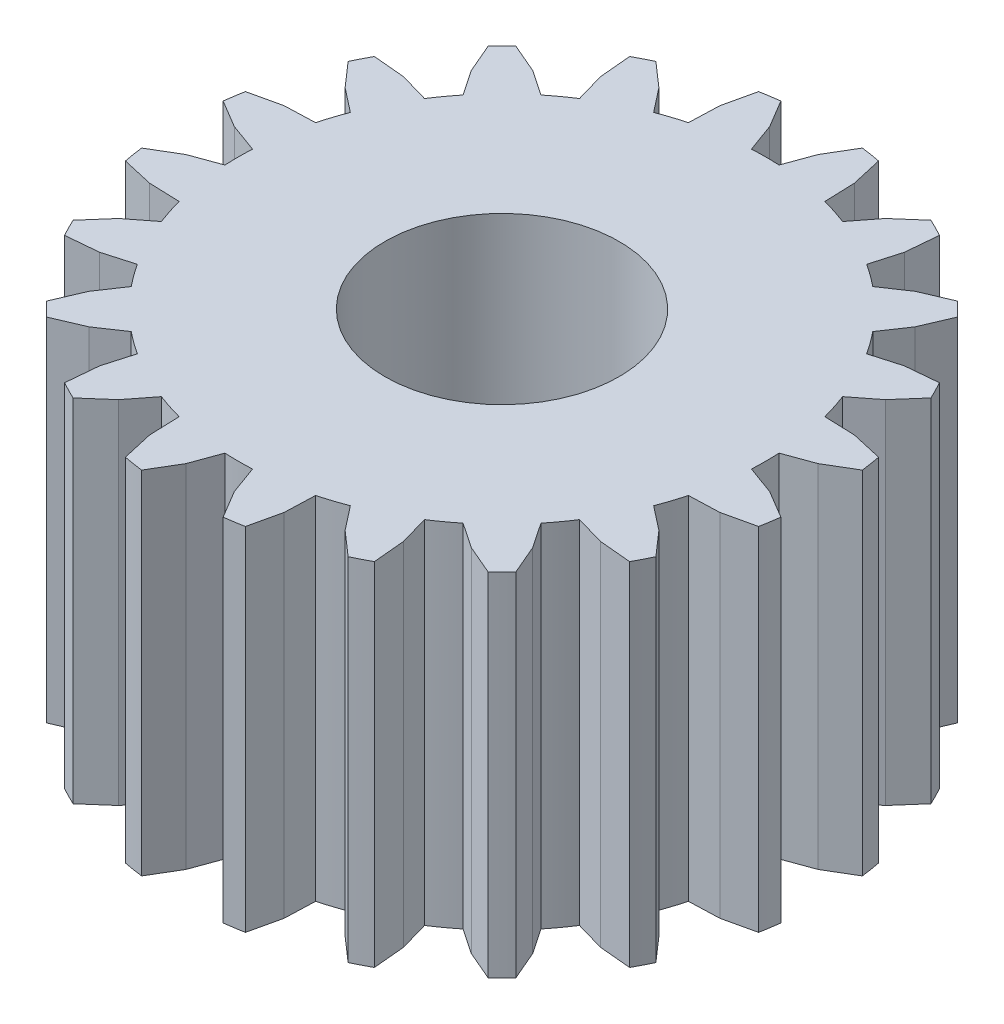
SolidWorks part; units mm, degrees
ref_plane "Ön Düzlem" through (0, 0, 0) normal (0, 0, 1) x (1, 0, 0)
ref_plane "Üst Düzlem" through (0, 0, 0) normal (0, 1, 0) x (1, 0, 0)
ref_plane "Sağ Düzlem" through (0, 0, 0) normal (1, 0, 0) x (0, 0, -1)
sketch "Çizim2" plane through (0, 0, 0) normal (0, 1, 0) x (1, 0, 0)
  line L0 (2.7279, -0.3477) -> (2.4914, -0.2068)
  line L1 (2.4914, -0.2068) -> (2.2469, -0.1178)
  line L2 (2.2469, 0.1178) -> (2.4914, 0.2068)
  line L3 (2.4914, 0.2068) -> (2.7279, 0.3477)
  line L4 (2.7019, 0.5123) -> (2.4334, 0.5733)
  line L5 (2.4334, 0.5733) -> (2.1733, 0.5823)
  line L6 (2.1006, 0.8063) -> (2.3056, 0.9665)
  line L7 (2.3056, 0.9665) -> (2.487, 1.1736)
  line L8 (2.4113, 1.3222) -> (2.1371, 1.2972)
  line L9 (2.1371, 1.2972) -> (1.887, 1.2254)
  line L10 (1.7486, 1.416) -> (1.8941, 1.6317)
  line L11 (1.8941, 1.6317) -> (2.0026, 1.8847)
  line L12 (1.8847, 2.0026) -> (1.6317, 1.8941)
  line L13 (1.6317, 1.8941) -> (1.416, 1.7486)
  line L14 (1.2254, 1.887) -> (1.2972, 2.1371)
  line L15 (1.2972, 2.1371) -> (1.3222, 2.4113)
  line L16 (1.1736, 2.487) -> (0.9665, 2.3056)
  line L17 (0.9665, 2.3056) -> (0.8063, 2.1006)
  line L18 (0.5823, 2.1733) -> (0.5733, 2.4334)
  line L19 (0.5733, 2.4334) -> (0.5123, 2.7019)
  line L20 (0.3477, 2.7279) -> (0.2068, 2.4914)
  line L21 (0.2068, 2.4914) -> (0.1178, 2.2469)
  line L22 (-0.1178, 2.2469) -> (-0.2068, 2.4914)
  line L23 (-0.2068, 2.4914) -> (-0.3477, 2.7279)
  line L24 (-0.5123, 2.7019) -> (-0.5733, 2.4334)
  line L25 (-0.5733, 2.4334) -> (-0.5823, 2.1733)
  line L26 (-0.8063, 2.1006) -> (-0.9665, 2.3056)
  line L27 (-0.9665, 2.3056) -> (-1.1736, 2.487)
  line L28 (-1.3222, 2.4113) -> (-1.2972, 2.1371)
  line L29 (-1.2972, 2.1371) -> (-1.2254, 1.887)
  line L30 (-1.416, 1.7486) -> (-1.6317, 1.8941)
  line L31 (-1.6317, 1.8941) -> (-1.8847, 2.0026)
  line L32 (-2.0026, 1.8847) -> (-1.8941, 1.6317)
  line L33 (-1.8941, 1.6317) -> (-1.7486, 1.416)
  line L34 (-1.887, 1.2254) -> (-2.1371, 1.2972)
  line L35 (-2.1371, 1.2972) -> (-2.4113, 1.3222)
  line L36 (-2.487, 1.1736) -> (-2.3056, 0.9665)
  line L37 (-2.3056, 0.9665) -> (-2.1006, 0.8063)
  line L38 (-2.1733, 0.5823) -> (-2.4334, 0.5733)
  line L39 (-2.4334, 0.5733) -> (-2.7019, 0.5123)
  line L40 (-2.7279, 0.3477) -> (-2.4914, 0.2068)
  line L41 (-2.4914, 0.2068) -> (-2.2469, 0.1178)
  line L42 (-2.2469, -0.1178) -> (-2.4914, -0.2068)
  line L43 (-2.4914, -0.2068) -> (-2.7279, -0.3477)
  line L44 (-2.7019, -0.5123) -> (-2.4334, -0.5733)
  line L45 (-2.4334, -0.5733) -> (-2.1733, -0.5823)
  line L46 (-2.1006, -0.8063) -> (-2.3056, -0.9665)
  line L47 (-2.3056, -0.9665) -> (-2.487, -1.1736)
  line L48 (-2.4113, -1.3222) -> (-2.1371, -1.2972)
  line L49 (-2.1371, -1.2972) -> (-1.887, -1.2254)
  line L50 (-1.7486, -1.416) -> (-1.8941, -1.6317)
  line L51 (-1.8941, -1.6317) -> (-2.0026, -1.8847)
  line L52 (-1.8847, -2.0026) -> (-1.6317, -1.8941)
  line L53 (-1.6317, -1.8941) -> (-1.416, -1.7486)
  line L54 (-1.2254, -1.887) -> (-1.2972, -2.1371)
  line L55 (-1.2972, -2.1371) -> (-1.3222, -2.4113)
  line L56 (-1.1736, -2.487) -> (-0.9665, -2.3056)
  line L57 (-0.9665, -2.3056) -> (-0.8063, -2.1006)
  line L58 (-0.5823, -2.1733) -> (-0.5733, -2.4334)
  line L59 (-0.5733, -2.4334) -> (-0.5123, -2.7019)
  line L60 (-0.3477, -2.7279) -> (-0.2068, -2.4914)
  line L61 (-0.2068, -2.4914) -> (-0.1178, -2.2469)
  line L62 (0.1178, -2.2469) -> (0.2068, -2.4914)
  line L63 (0.2068, -2.4914) -> (0.3477, -2.7279)
  line L64 (0.5123, -2.7019) -> (0.5733, -2.4334)
  line L65 (0.5733, -2.4334) -> (0.5823, -2.1733)
  line L66 (0.8063, -2.1006) -> (0.9665, -2.3056)
  line L67 (0.9665, -2.3056) -> (1.1736, -2.487)
  line L68 (1.3222, -2.4113) -> (1.2972, -2.1371)
  line L69 (1.2972, -2.1371) -> (1.2254, -1.887)
  line L70 (1.416, -1.7486) -> (1.6317, -1.8941)
  line L71 (1.6317, -1.8941) -> (1.8847, -2.0026)
  line L72 (2.0026, -1.8847) -> (1.8941, -1.6317)
  line L73 (1.8941, -1.6317) -> (1.7486, -1.416)
  line L74 (1.887, -1.2254) -> (2.1371, -1.2972)
  line L75 (2.1371, -1.2972) -> (2.4113, -1.3222)
  line L76 (2.487, -1.1736) -> (2.3056, -0.9665)
  line L77 (2.3056, -0.9665) -> (2.1006, -0.8063)
  line L78 (2.1733, -0.5823) -> (2.4334, -0.5733)
  line L79 (2.4334, -0.5733) -> (2.7019, -0.5123)
  circle A0 centre (0, 0) radius 1
  circle A1 centre (0, 0) radius 2
  arc A2 (2.2469, -0.1178) -> (2.2469, 0.1178) centre (0, 0) ccw
  arc A3 (2.7279, 0.3477) -> (2.7019, 0.5123) centre (0, 0) ccw
  arc A4 (2.1733, 0.5823) -> (2.1006, 0.8063) centre (0, 0) ccw
  arc A5 (2.487, 1.1736) -> (2.4113, 1.3222) centre (0, 0) ccw
  arc A6 (1.887, 1.2254) -> (1.7486, 1.416) centre (0, 0) ccw
  arc A7 (2.0026, 1.8847) -> (1.8847, 2.0026) centre (0, 0) ccw
  arc A8 (1.416, 1.7486) -> (1.2254, 1.887) centre (0, 0) ccw
  arc A9 (1.3222, 2.4113) -> (1.1736, 2.487) centre (0, 0) ccw
  arc A10 (0.8063, 2.1006) -> (0.5823, 2.1733) centre (0, 0) ccw
  arc A11 (0.5123, 2.7019) -> (0.3477, 2.7279) centre (0, 0) ccw
  arc A12 (0.1178, 2.2469) -> (-0.1178, 2.2469) centre (0, 0) ccw
  arc A13 (-0.3477, 2.7279) -> (-0.5123, 2.7019) centre (0, 0) ccw
  arc A14 (-0.5823, 2.1733) -> (-0.8063, 2.1006) centre (0, 0) ccw
  arc A15 (-1.1736, 2.487) -> (-1.3222, 2.4113) centre (0, 0) ccw
  arc A16 (-1.2254, 1.887) -> (-1.416, 1.7486) centre (0, 0) ccw
  arc A17 (-1.8847, 2.0026) -> (-2.0026, 1.8847) centre (0, 0) ccw
  arc A18 (-1.7486, 1.416) -> (-1.887, 1.2254) centre (0, 0) ccw
  arc A19 (-2.4113, 1.3222) -> (-2.487, 1.1736) centre (0, 0) ccw
  arc A20 (-2.1006, 0.8063) -> (-2.1733, 0.5823) centre (0, 0) ccw
  arc A21 (-2.7019, 0.5123) -> (-2.7279, 0.3477) centre (0, 0) ccw
  arc A22 (-2.2469, 0.1178) -> (-2.2469, -0.1178) centre (0, 0) ccw
  arc A23 (-2.7279, -0.3477) -> (-2.7019, -0.5123) centre (0, 0) ccw
  arc A24 (-2.1733, -0.5823) -> (-2.1006, -0.8063) centre (0, 0) ccw
  arc A25 (-2.487, -1.1736) -> (-2.4113, -1.3222) centre (0, 0) ccw
  arc A26 (-1.887, -1.2254) -> (-1.7486, -1.416) centre (0, 0) ccw
  arc A27 (-2.0026, -1.8847) -> (-1.8847, -2.0026) centre (0, 0) ccw
  arc A28 (-1.416, -1.7486) -> (-1.2254, -1.887) centre (0, 0) ccw
  arc A29 (-1.3222, -2.4113) -> (-1.1736, -2.487) centre (0, 0) ccw
  arc A30 (-0.8063, -2.1006) -> (-0.5823, -2.1733) centre (0, 0) ccw
  arc A31 (-0.5123, -2.7019) -> (-0.3477, -2.7279) centre (0, 0) ccw
  arc A32 (-0.1178, -2.2469) -> (0.1178, -2.2469) centre (0, 0) ccw
  arc A33 (0.3477, -2.7279) -> (0.5123, -2.7019) centre (0, 0) ccw
  arc A34 (0.5823, -2.1733) -> (0.8063, -2.1006) centre (0, 0) ccw
  arc A35 (1.1736, -2.487) -> (1.3222, -2.4113) centre (0, 0) ccw
  arc A36 (1.2254, -1.887) -> (1.416, -1.7486) centre (0, 0) ccw
  arc A37 (1.8847, -2.0026) -> (2.0026, -1.8847) centre (0, 0) ccw
  arc A38 (1.7486, -1.416) -> (1.887, -1.2254) centre (0, 0) ccw
  arc A39 (2.4113, -1.3222) -> (2.487, -1.1736) centre (0, 0) ccw
  arc A40 (2.1006, -0.8063) -> (2.1733, -0.5823) centre (0, 0) ccw
  arc A41 (2.7019, -0.5123) -> (2.7279, -0.3477) centre (0, 0) ccw
extrude "Yükseklik-Ekstrüzyon1" add sketch "Çizim2" along normal blind 3 contours L79 A41 L0 L1 A2 L2 L3 A3 L4 L5 A4 L6 L7 A5 L8 L9 A6 L10 L11 A7 L12 L13 A8 L14 L15 A9 L16 L17 A10 L18 L19 A11 L20 L21 A12 L22 L23 A13 L24 L25 A14 L26 L27 A15 L28 L29 A16 L30 L31 A17 L32 | A1 A0
